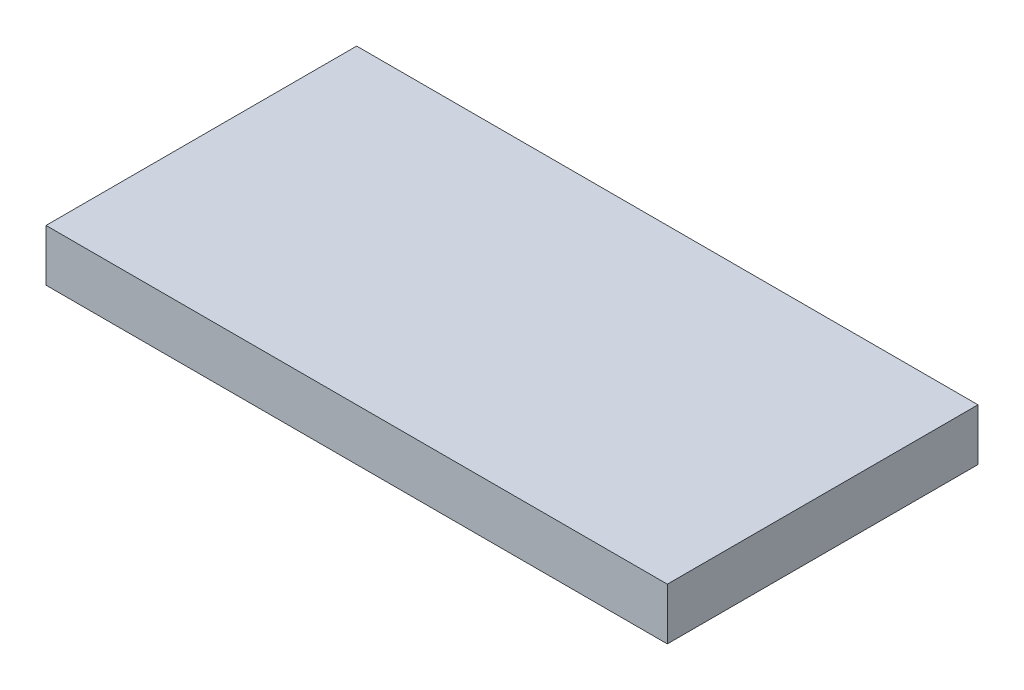
SolidWorks part; units mm, degrees
ref_plane "Front Plane" through (0, 0, 0) normal (0, 0, 1) x (1, 0, 0)
ref_plane "Top Plane" through (0, 0, 0) normal (0, 1, 0) x (1, 0, 0)
ref_plane "Right Plane" through (0, 0, 0) normal (1, 0, 0) x (0, 0, -1)
sketch "Sketch1" plane through (0, 0, 0) normal (0, 1, 0) x (1, 0, 0)
  line L1 (0, 0) -> (60, 0)
  line L2 (0, 0) -> (0, 30)
  line L3 (0, 30) -> (60, 30)
  line L4 (60, 0) -> (60, 30)
  dimension "D1" = 60
  dimension "D2" = 30
extrude "Boss-Extrude1" add sketch "Sketch1" along normal blind 5
